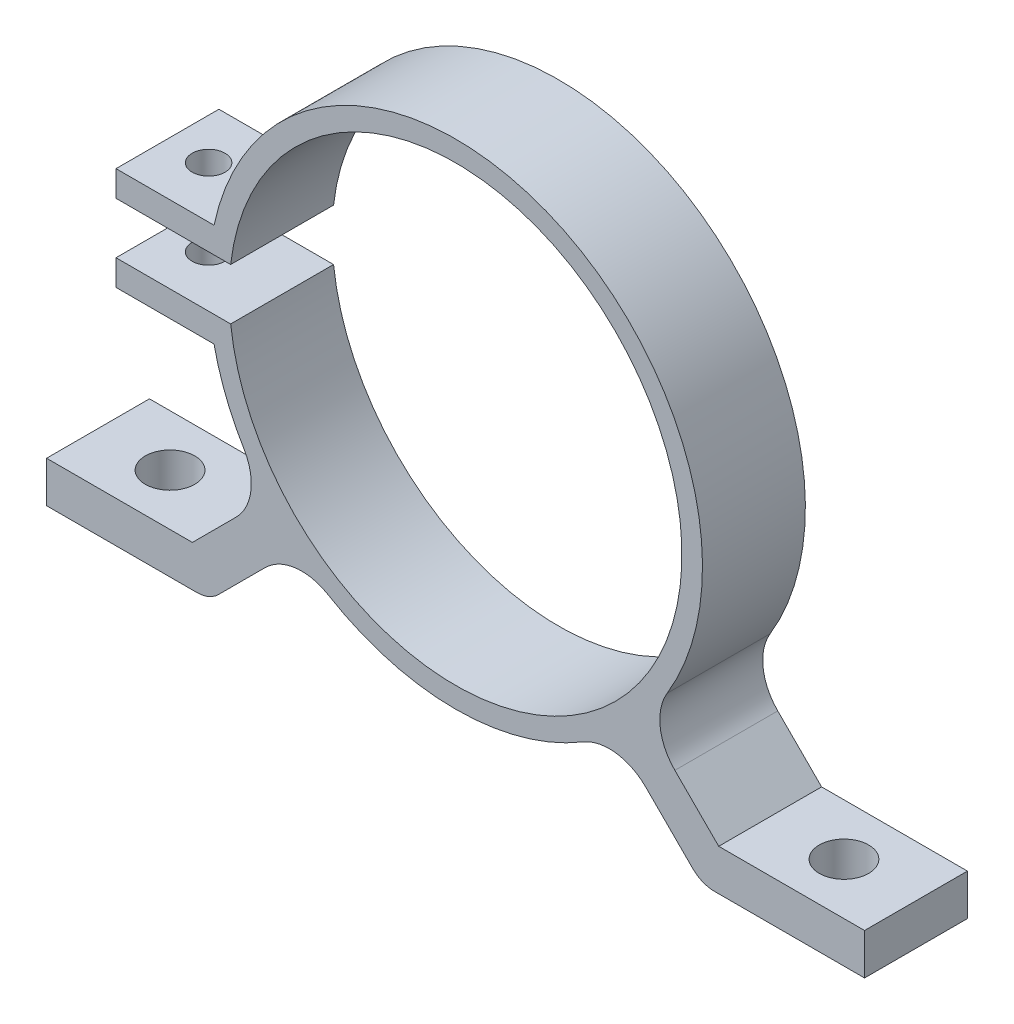
SolidWorks part; units mm, degrees
ref_plane "Front Plane" through (0, 0, 0) normal (0, 0, 1) x (1, 0, 0)
ref_plane "Top Plane" through (0, 0, 0) normal (0, 1, 0) x (1, 0, 0)
ref_plane "Right Plane" through (0, 0, 0) normal (1, 0, 0) x (0, 0, -1)
sketch "Sketch1" plane through (0, 0, 0) normal (0, 0, 1) x (1, 0, 0)
  line L0 (0, 0) -> (0, -50000) construction
  circle A1 centre (0, 0) radius 24
  dimension "D2" = 48
extrude "Boss-Extrude1" add sketch "Sketch1" along normal mid plane 10 contours A1
sketch "Sketch2" plane through (0, 0, 0) normal (0, 0, 1) x (1, 0, 0)
  line L0 (0, 0) -> (24.4558, -24.4558)
  line L1 (25.163, -24.7487) -> (39.7487, -24.7487)
  line L2 (0, 0) -> (-24.4558, -24.4558)
  line L3 (-25.163, -24.7487) -> (-39.7487, -24.7487)
  line L4 (0, 0) -> (0, -50000) construction
  arc A1 (24.4558, -24.4558) -> (25.163, -24.7487) centre (25.163, -23.7487) ccw
  arc A2 (-24.4558, -24.4558) -> (-25.163, -24.7487) centre (-25.163, -23.7487) cw
  point P12 (-24.7487, -24.7487)
  dimension "D5" = 1
  dimension "D1" = 15
  dimension "D2" = 45
  dimension "D3" = 35
  dimension "D4" = 45
extrude "Extrude-Thin1" add sketch "Sketch2" along normal mid plane 10 thin
sketch "Sketch4" plane through (0, 0, 0) normal (0, 0, 1) x (1, 0, 0)
  line L1 (-33, 5) -> (0, 5)
  line L2 (-33, 5) -> (-33, -5)
  line L3 (-33, -5) -> (0, -5)
  line L4 (0, 5) -> (0, -5)
  line L5 (-33, 5) -> (0, -5) construction
  line L6 (-33, -5) -> (0, 5) construction
  point P0 (-16.5, 0)
  dimension "D1" = 33
  dimension "D2" = 10
extrude "Boss-Extrude2" add sketch "Sketch4" along normal mid plane 10
sketch "Sketch5" plane through (0, 0, 5) normal (0, 0, 1) x (1, 0, 0)
  line L0 (-33, 5) -> (-33, -5) construction
  line L1 (-33, 2.5) -> (0, 2.5)
  line L2 (-33, 2.5) -> (-33, -2.5)
  line L3 (-33, -2.5) -> (0, -2.5)
  line L4 (0, 2.5) -> (0, -2.5)
  line L5 (-33, 2.5) -> (0, -2.5) construction
  line L6 (-33, -2.5) -> (0, 2.5) construction
  circle A0 centre (0, 0) radius 22
  point P6 (-16.5, 0)
  dimension "D1" = 44
  dimension "D2" = 5
extrude "Cut-Extrude1" cut sketch "Sketch5" against normal blind 26.5 contours A0 | L3 L4 L1 L2
sketch "Sketch6" plane through (0, 5, 0) normal (0, 1, 0) x (1, 0, 0)
  line L0 (-33, -5) -> (-33, 5) construction
  circle A0 centre (-29, 0) radius 1.6
  dimension "D1" = 3.2
  dimension "D2" = 4
extrude "Cut-Extrude2" cut sketch "Sketch6" against normal up to surface (10 mm away) and the other way through all up to face at (-28.2367, -5, 0)
sketch "Sketch7" plane through (0, -22.7487, 0) normal (0, 1, 0) x (1, 0, 0)
  line L1 (-39.7487, -5) -> (-39.7487, 5) construction
  line L2 (39.7487, -5) -> (39.7487, 5) construction
  circle A0 centre (-32.7487, 0) radius 2.4
  circle A1 centre (32.7487, 0) radius 2.4
  dimension "D1" = 4.8
  dimension "D2" = 7
  dimension "D3" = 7
extrude "Cut-Extrude3" cut sketch "Sketch7" against normal through all
fillet "Fillet3" radius 5 4 edges at (18.3257, -15.4973, 0) (15.4973, -18.3257, 0) (-18.3257, -15.4973, 0) (-15.4973, -18.3257, 0)
